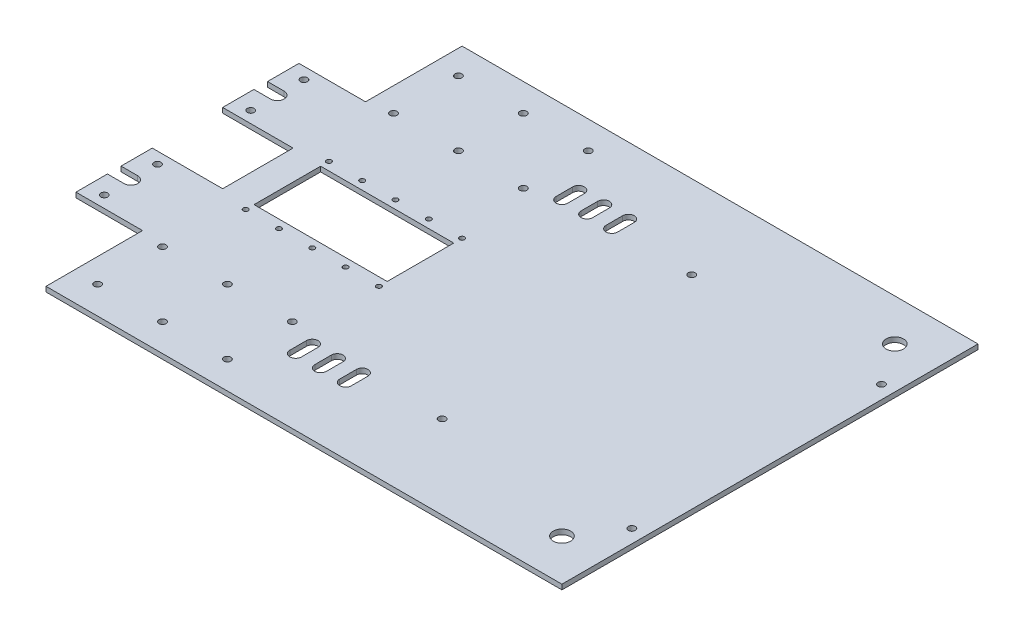
SolidWorks part; units mm, degrees
ref_plane "Plan de face" through (0, 0, 0) normal (0, 0, 1) x (1, 0, 0)
ref_plane "Plan de dessus" through (0, 0, 0) normal (0, 1, 0) x (1, 0, 0)
ref_plane "Plan de droite" through (0, 0, 0) normal (1, 0, 0) x (0, 0, -1)
ref_plane "Plan1" through (0, 3, 0) normal (0, 1, 0) x (1, 0, 0)
sketch "Esquisse1" plane through (0, 3, 0) normal (0, 1, 0) x (1, 0, 0)
  line L0 (0, -103.85) -> (42.3, -103.85)
  line L1 (42.3, -103.85) -> (42.3, -146.15)
  line L2 (42.3, -146.15) -> (0, -146.15)
  line L3 (0, -146.15) -> (0, -164.9)
  line L4 (0, -164.9) -> (10, -164.9)
  line L5 (10, -173.1) -> (0, -173.1)
  line L6 (0, -173.1) -> (0, -250)
  line L7 (0, -250) -> (350, -250)
  line L8 (350, -250) -> (350, 0)
  line L9 (350, 0) -> (0, 0)
  line L10 (0, 0) -> (0, -76.9)
  line L11 (0, -76.9) -> (10, -76.9)
  line L12 (10, -85.1) -> (0, -85.1)
  line L13 (0, -85.1) -> (0, -103.85)
  line L18 (140, -145) -> (60, -145)
  line L19 (60, -145) -> (60, -105)
  line L20 (60, -105) -> (140, -105)
  line L21 (140, -105) -> (140, -145)
  arc A0 (10, -164.9) -> (10, -173.1) centre (10, -169) cw
  arc A1 (10, -76.9) -> (10, -85.1) centre (10, -81) cw
  circle A2 centre (101.2, -181.6) radius 1.6 construction
  circle A3 centre (38.8, -194.4) radius 1.6 construction
  circle A4 centre (54.4, -181.6) radius 1.6 construction
  circle A5 centre (54.4, -207.2) radius 1.6 construction
  circle A6 centre (54.4, -220) radius 1.6 construction
  circle A7 centre (38.8, -220) radius 1.6 construction
  circle A8 centre (54.4, -194.4) radius 1.6 construction
  circle A9 centre (101.2, -30) radius 1.6 construction
  circle A10 centre (101.2, -68.4) radius 1.6 construction
  circle A15 centre (38.8, -55.6) radius 1.6 construction
  circle A16 centre (38.8, -42.8) radius 1.6 construction
  circle A17 centre (54.4, -55.6) radius 1.6 construction
  circle A18 centre (54.4, -30) radius 1.6 construction
  circle A19 centre (54.4, -68.4) radius 1.6 construction
  circle A20 centre (38.8, -30) radius 1.6 construction
  circle A21 centre (54.4, -42.8) radius 1.6 construction
  circle A22 centre (38.8, -68.4) radius 1.6 construction
  circle A23 centre (70, -30) radius 1.6 construction
  circle A24 centre (85.6, -30) radius 1.6 construction
  circle A25 centre (70, -42.8) radius 1.6 construction
  circle A26 centre (85.6, -42.8) radius 1.6 construction
  circle A27 centre (70, -55.6) radius 1.6 construction
  circle A28 centre (85.6, -55.6) radius 1.6 construction
  circle A29 centre (70, -68.4) radius 1.6 construction
  circle A30 centre (85.6, -68.4) radius 1.6 construction
  circle A31 centre (101.2, -42.8) radius 1.6 construction
  circle A32 centre (101.2, -55.6) radius 1.6 construction
  circle A49 centre (140, -150) radius 1.5
  circle A50 centre (120, -150) radius 1.5
  circle A51 centre (100, -150) radius 1.5
  circle A52 centre (80, -150) radius 1.5
  circle A53 centre (60, -150) radius 1.5
  circle A59 centre (140, -100) radius 1.5
  circle A60 centre (120, -100) radius 1.5
  circle A61 centre (100, -100) radius 1.5
  circle A62 centre (80, -100) radius 1.5
  circle A63 centre (60, -100) radius 1.5
  circle A64 centre (325, -225) radius 5.25
  circle A65 centre (325, -25) radius 5.25
  circle A66 centre (10, -97) radius 2.1
  circle A67 centre (10, -153) radius 2.1
  circle A68 centre (10, -185) radius 2.1
  circle A69 centre (10, -65) radius 2.1
  circle A74 centre (85.6, -181.6) radius 1.6 construction
  circle A75 centre (70, -181.6) radius 1.6 construction
  circle A76 centre (101.2, -194.4) radius 1.6 construction
  circle A77 centre (85.6, -194.4) radius 1.6 construction
  circle A78 centre (70, -194.4) radius 1.6 construction
  circle A79 centre (101.2, -207.2) radius 1.6 construction
  circle A80 centre (85.6, -207.2) radius 1.6 construction
  circle A81 centre (70, -207.2) radius 1.6 construction
  circle A82 centre (101.2, -220) radius 1.6 construction
  circle A83 centre (85.6, -220) radius 1.6 construction
  circle A84 centre (70, -220) radius 1.6 construction
  circle A85 centre (38.8, -181.6) radius 1.6 construction
  circle A86 centre (38.8, -207.2) radius 1.6 construction
extrude "Boss.-Extru.1" add sketch "Esquisse1" against normal blind 3
sketch "Esquisse3" plane through (0, 3, 0) normal (0, 1, 0) x (1, 0, 0)
  line L8 (160, -145) -> (240, -145)
  line L9 (160, -105) -> (160, -145)
  line L10 (240, -105) -> (160, -105)
  line L11 (240, -145) -> (240, -105)
  line L16 (60, -145) -> (140, -145)
  line L17 (60, -105) -> (60, -145)
  line L18 (140, -105) -> (60, -105)
  line L19 (140, -145) -> (140, -105)
  line L36 (10, -85.1) -> (0, -85.1)
  line L37 (0, -85.1) -> (0, -103.85)
  line L38 (0, -103.85) -> (42.3, -103.85)
  line L39 (42.3, -103.85) -> (42.3, -146.15)
  line L40 (42.3, -146.15) -> (0, -146.15)
  line L41 (0, -146.15) -> (0, -164.9)
  line L42 (0, -164.9) -> (10, -164.9)
  line L43 (10, -173.1) -> (0, -173.1)
  line L44 (0, -173.1) -> (0, -250)
  line L45 (0, -250) -> (350, -250)
  line L46 (350, -250) -> (350, 0)
  line L47 (350, 0) -> (0, 0)
  line L48 (0, 0) -> (0, -76.9)
  line L49 (0, -76.9) -> (10, -76.9)
  circle A2 centre (54.4, -220) radius 1.6
  circle A4 centre (54.4, -207.2) radius 1.6
  circle A6 centre (54.4, -181.6) radius 1.6
  circle A8 centre (38.8, -194.4) radius 1.6
  circle A10 centre (101.2, -181.6) radius 1.6
  arc A14 (10, -173.1) -> (10, -164.9) centre (10, -169) ccw
  arc A15 (10, -85.1) -> (10, -76.9) centre (10, -81) ccw
  circle A16 centre (150, -225) radius 2.1
  circle A18 centre (200, -175) radius 2.1
  circle A20 centre (250, -175) radius 2.1
  circle A22 centre (300, -175) radius 2.1
  circle A24 centre (101.2, -68.4) radius 1.6
  circle A26 centre (101.2, -30) radius 1.6
  circle A28 centre (54.4, -194.4) radius 1.6
  circle A30 centre (38.8, -220) radius 1.6
  circle A32 centre (38.8, -68.4) radius 1.6
  circle A34 centre (54.4, -42.8) radius 1.6
  circle A36 centre (38.8, -30) radius 1.6
  circle A38 centre (54.4, -68.4) radius 1.6
  circle A40 centre (54.4, -30) radius 1.6
  circle A42 centre (54.4, -55.6) radius 1.6
  circle A44 centre (38.8, -42.8) radius 1.6
  circle A46 centre (38.8, -55.6) radius 1.6
  circle A48 centre (85.6, -68.4) radius 1.6
  circle A50 centre (70, -68.4) radius 1.6
  circle A52 centre (85.6, -55.6) radius 1.6
  circle A54 centre (70, -55.6) radius 1.6
  circle A56 centre (85.6, -42.8) radius 1.6
  circle A58 centre (70, -42.8) radius 1.6
  circle A60 centre (85.6, -30) radius 1.6
  circle A62 centre (70, -30) radius 1.6
  circle A64 centre (250, -75) radius 2.1
  circle A66 centre (200, -75) radius 2.1
  circle A68 centre (150, -75) radius 2.1
  circle A70 centre (300, -125) radius 2.1
  circle A72 centre (250, -125) radius 2.1
  circle A74 centre (150, -125) radius 2.1
  circle A76 centre (101.2, -55.6) radius 1.6
  circle A78 centre (101.2, -42.8) radius 1.6
  circle A80 centre (200, -150) radius 1.5
  circle A82 centre (220, -150) radius 1.5
  circle A84 centre (240, -150) radius 1.5
  circle A86 centre (300, -25) radius 2.1
  circle A88 centre (250, -25) radius 2.1
  circle A90 centre (200, -25) radius 2.1
  circle A92 centre (150, -25) radius 2.1
  circle A94 centre (300, -75) radius 2.1
  circle A96 centre (240, -100) radius 1.5
  circle A98 centre (60, -150) radius 1.5
  circle A100 centre (80, -150) radius 1.5
  circle A102 centre (100, -150) radius 1.5
  circle A104 centre (120, -150) radius 1.5
  circle A106 centre (140, -150) radius 1.5
  circle A108 centre (160, -150) radius 1.5
  circle A110 centre (180, -150) radius 1.5
  circle A112 centre (80, -100) radius 1.5
  circle A114 centre (100, -100) radius 1.5
  circle A116 centre (120, -100) radius 1.5
  circle A118 centre (140, -100) radius 1.5
  circle A120 centre (160, -100) radius 1.5
  circle A122 centre (180, -100) radius 1.5
  circle A124 centre (200, -100) radius 1.5
  circle A126 centre (220, -100) radius 1.5
  circle A128 centre (10, -185) radius 2.1
  circle A130 centre (10, -153) radius 2.1
  circle A132 centre (10, -97) radius 2.1
  circle A134 centre (325, -25) radius 5.25
  circle A136 centre (325, -225) radius 5.25
  circle A138 centre (60, -100) radius 1.5
  circle A140 centre (101.2, -194.4) radius 1.6
  circle A142 centre (70, -181.6) radius 1.6
  circle A144 centre (85.6, -181.6) radius 1.6
  circle A146 centre (250, -225) radius 2.1
  circle A148 centre (200, -225) radius 2.1
  circle A150 centre (300, -225) radius 2.1
  circle A152 centre (150, -175) radius 2.1
  circle A154 centre (10, -65) radius 2.1
  circle A156 centre (70, -220) radius 1.6
  circle A158 centre (85.6, -220) radius 1.6
  circle A160 centre (101.2, -220) radius 1.6
  circle A162 centre (70, -207.2) radius 1.6
  circle A164 centre (85.6, -207.2) radius 1.6
  circle A166 centre (101.2, -207.2) radius 1.6
  circle A168 centre (70, -194.4) radius 1.6
  circle A170 centre (85.6, -194.4) radius 1.6
  circle A172 centre (38.8, -207.2) radius 1.6
  circle A174 centre (38.8, -181.6) radius 1.6
extrude "Boss.-Extru.2" [suppressed] add sketch "Esquisse3" against normal blind 3
sketch "Esquisse2" plane through (0, 3, 0) normal (0, 1, 0) x (1, 0, 0)
  line L0 (350, -250) -> (350, 0) construction
  line L1 (42.3, -125) -> (389.8045, -125) construction
  line L2 (228, -200) -> (342, -200) construction
  line L3 (350, -250) -> (350, 0) construction
  line L4 (150, -16.6) -> (150, -223.3616) construction
  line L6 (228, -200) -> (228, -50) construction
  line L7 (228, -50) -> (342, -50) construction
  line L8 (342, -200) -> (342, -50) construction
  line L9 (0, -173.1) -> (0, -250) construction
  line L15 (150, -40) -> (150, -50) construction
  line L16 (153.5, -40) -> (153.5, -50)
  line L17 (146.5, -40) -> (146.5, -50)
  line L18 (161.5, -40) -> (161.5, -50)
  line L19 (168.5, -40) -> (168.5, -50)
  line L20 (165, -40) -> (165, -50) construction
  line L21 (176.5, -40) -> (176.5, -50)
  line L22 (183.5, -40) -> (183.5, -50)
  line L23 (180, -40) -> (180, -50) construction
  line L24 (180, -210) -> (180, -200) construction
  line L25 (183.5, -210) -> (183.5, -200)
  line L26 (176.5, -210) -> (176.5, -200)
  line L27 (165, -210) -> (165, -200) construction
  line L28 (168.5, -210) -> (168.5, -200)
  line L29 (161.5, -210) -> (161.5, -200)
  line L30 (150, -210) -> (150, -200) construction
  line L31 (153.5, -210) -> (153.5, -200)
  line L32 (146.5, -210) -> (146.5, -200)
  line L39 (0, -192) -> (40, -192)
  line L40 (0, 0) -> (40, 0)
  line L41 (0, 0) -> (0, -58)
  line L42 (0, -58) -> (40, -58)
  line L43 (40, 0) -> (40, -58)
  line L44 (40, -250) -> (40, -192)
  line L45 (0, -250) -> (40, -250)
  line L46 (0, -250) -> (0, -192)
  circle A0 centre (54.4, -194.4) radius 2.1
  circle A1 centre (93.4, -194.4) radius 2.1
  circle A2 centre (93.4, -233.4) radius 2.1
  circle A3 centre (54.4, -233.4) radius 2.1
  circle A4 centre (54.4, -16.6) radius 2.1
  circle A5 centre (93.4, -16.6) radius 2.1
  circle A6 centre (93.4, -55.6) radius 2.1
  circle A7 centre (54.4, -55.6) radius 2.1
  circle A26 centre (342, -200) radius 2.1
  circle A28 centre (342, -50) radius 2.1
  circle A30 centre (228, -50) radius 2.1
  arc A31 (153.5, -40) -> (146.5, -40) centre (150, -40) ccw
  circle A32 centre (228, -200) radius 2.1
  arc A33 (146.5, -50) -> (153.5, -50) centre (150, -50) ccw
  arc A34 (168.5, -40) -> (161.5, -40) centre (165, -40) ccw
  arc A35 (161.5, -50) -> (168.5, -50) centre (165, -50) ccw
  arc A36 (183.5, -40) -> (176.5, -40) centre (180, -40) ccw
  arc A37 (176.5, -50) -> (183.5, -50) centre (180, -50) ccw
  arc A38 (183.5, -210) -> (176.5, -210) centre (180, -210) cw
  arc A39 (176.5, -200) -> (183.5, -200) centre (180, -200) cw
  arc A40 (168.5, -210) -> (161.5, -210) centre (165, -210) cw
  arc A41 (161.5, -200) -> (168.5, -200) centre (165, -200) cw
  arc A42 (153.5, -210) -> (146.5, -210) centre (150, -210) cw
  arc A43 (146.5, -200) -> (153.5, -200) centre (150, -200) cw
  circle A44 centre (132.4, -16.6) radius 2.1
  circle A45 centre (132.4, -55.6) radius 2.1
  circle A46 centre (132.4, -194.4) radius 2.1
  circle A47 centre (132.4, -233.4) radius 2.1
  point P13 (350, -125)
  point P27 (150, -45)
  point P35 (165, -45)
  point P43 (180, -45)
  point P49 (180, -205)
  point P56 (165, -205)
  point P61 (228, -125)
  point P73 (150, -205)
  dimension "D1" = 4.2
  dimension "D21" = 4.2
  dimension "D22" = 4.2
  dimension "D23" = 4.2
  dimension "D24" = 4.2
  dimension "D7" = 3.5
  dimension "D4" = 39
  dimension "D5" = 39
  dimension "D18" = 8
  dimension "D19" = 114
  dimension "D20" = 150
  dimension "D30" = 69.4
  dimension "D31" = 54.4
  dimension "D8" = 10
  dimension "D9" = 80
  dimension "D10" = 15
  dimension "D6" = 78
  dimension "D12" = 40
  dimension "D13" = 58
  dimension "D15" = 39
  dimension "D2" = 2
  dimension "D3" = 2
  dimension "D11" = 3
  dimension "D14" = 2
extrude "Enlèv. mat.-Extru.1" cut sketch "Esquisse2" against normal up to next
sketch "Esquisse4" plane through (0, 0, 0) normal (0, -1, 0) x (1, 0, 0)
  line L0 (350, 125) -> (416.2171, 125) construction
  line L1 (270, 10) -> (202, 10) construction
  line L2 (270, 10) -> (270, 68) construction
  line L3 (270, 68) -> (202, 68) construction
  line L4 (202, 10) -> (202, 68) construction
  line L5 (204, 159) -> (204, 91) construction
  line L6 (350, 0) -> (40, 0) construction
  line L7 (350, 250) -> (350, 0) construction
  line L8 (345, 159) -> (287, 159) construction
  line L9 (345, 159) -> (345, 91) construction
  line L10 (345, 91) -> (287, 91) construction
  line L11 (287, 159) -> (287, 91) construction
  line L12 (262, 159) -> (204, 159) construction
  line L13 (262, 159) -> (262, 91) construction
  line L14 (262, 91) -> (204, 91) construction
  line L15 (270, 182) -> (202, 182) construction
  line L16 (270, 182) -> (270, 240) construction
  line L17 (270, 240) -> (202, 240) construction
  line L18 (202, 182) -> (202, 240) construction
  line L19 (40, 250) -> (350, 250) construction
  circle A0 centre (325, 25) radius 5.25 construction
  circle A1 centre (202, 68) radius 2.1
  circle A2 centre (270, 68) radius 2.1
  circle A3 centre (270, 10) radius 2.1
  circle A4 centre (202, 10) radius 2.1
  circle A6 centre (287, 159) radius 2.1
  circle A7 centre (345, 159) radius 2.1
  circle A8 centre (345, 91) radius 2.1
  circle A9 centre (287, 91) radius 2.1
  circle A10 centre (204, 159) radius 2.1
  circle A11 centre (262, 159) radius 2.1
  circle A12 centre (262, 91) radius 2.1
  circle A13 centre (204, 91) radius 2.1
  circle A14 centre (202, 240) radius 2.1
  circle A15 centre (270, 240) radius 2.1
  circle A16 centre (270, 182) radius 2.1
  circle A17 centre (202, 182) radius 2.1
  point P12 (350, 125)
  point P14 (287, 125)
  dimension "D14" = 2
  dimension "D5" = 4.2
  dimension "D11" = 4.2
  dimension "D1" = 68
  dimension "D2" = 58
  dimension "D3" = 55
  dimension "D4" = 10
  dimension "D8" = 68
  dimension "D9" = 58
  dimension "D10" = 5
  dimension "D15" = 25
  dimension "D17" = 10
  dimension "D6" = 2
  dimension "D7" = 2
  dimension "D12" = 2
  dimension "D13" = 2
  dimension "D16" = 2
extrude "Enlèv. mat.-Extru.2" [suppressed] cut sketch "Esquisse4" against normal up to next
equation "\"D22@Esquisse2\"=\"D21@Esquisse2\""
equation "\"D23@Esquisse2\"=\"D21@Esquisse2\""
equation "\"D24@Esquisse2\"=\"D21@Esquisse2\""
equation "\"D17@Esquisse4\"=\"D4@Esquisse4\""
